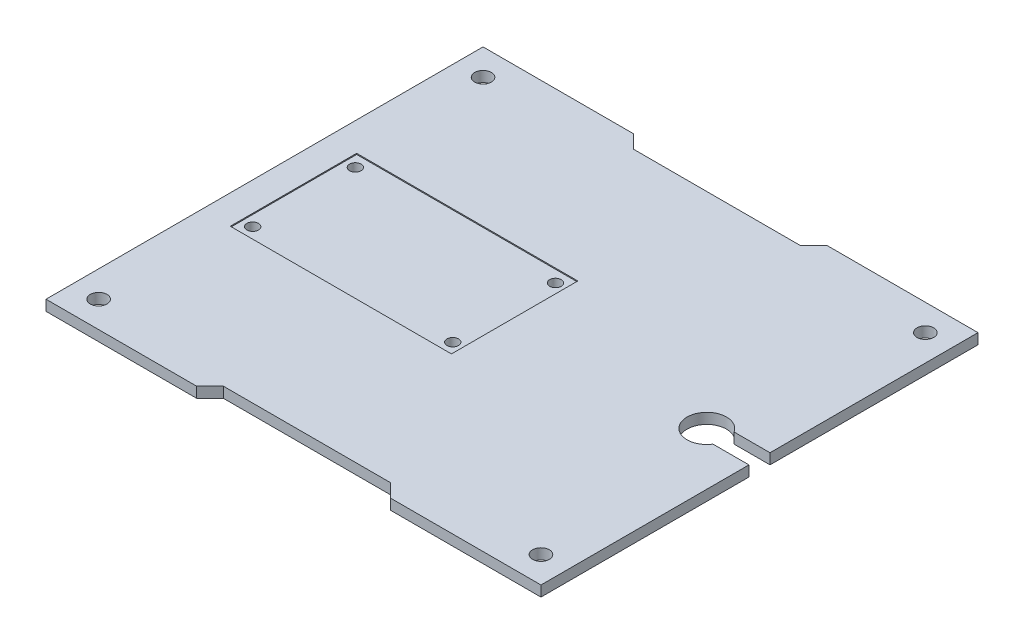
SolidWorks part; units mm, degrees
ref_plane "Front Plane" through (0, 0, 0) normal (0, 0, 1) x (1, 0, 0)
ref_plane "Top Plane" through (0, 0, 0) normal (0, 1, 0) x (1, 0, 0)
ref_plane "Right Plane" through (0, 0, 0) normal (1, 0, 0) x (0, 0, -1)
sketch "Sketch1" plane through (0, 0, 0) normal (0, 1, 0) x (1, 0, 0)
  line L1 (-47, -41.5) -> (47, -41.5)
  line L2 (-47, -41.5) -> (-47, 41.5)
  line L3 (-47, 41.5) -> (47, 41.5)
  line L4 (47, -41.5) -> (47, 41.5)
  line L5 (-47, -41.5) -> (47, 41.5) construction
  line L6 (-47, 41.5) -> (47, -41.5) construction
  line L7 (-42, -36.5) -> (42, -36.5) construction
  line L8 (-42, -36.5) -> (-42, 36.5) construction
  line L9 (-42, 36.5) -> (42, 36.5) construction
  line L10 (42, -36.5) -> (42, 36.5) construction
  line L11 (-42, -36.5) -> (42, 36.5) construction
  line L12 (-42, 36.5) -> (42, -36.5) construction
  circle A0 centre (-42, 36.5) radius 1.5875
  circle A1 centre (42, 36.5) radius 1.5875
  circle A2 centre (42, -36.5) radius 1.5875
  circle A3 centre (-42, -36.5) radius 1.5875
  point P0 (0, 0)
  point P14 (0, 0)
  dimension "D3" = 3.175
  dimension "D1" = 83
  dimension "D2" = 94
  dimension "D4" = 5
  dimension "D5" = 5
extrude "Boss-Extrude1" add sketch "Sketch1" along normal blind 2
sketch "Sketch2" plane through (0, 2, 0) normal (0, 1, 0) x (1, 0, 0)
  line L0 (0, 0) -> (-20.5, 0) construction
  line L1 (-39.5, 9.75) -> (-1.5, 9.75) construction
  line L2 (-39.5, 9.75) -> (-39.5, -9.75) construction
  line L3 (-39.5, -9.75) -> (-1.5, -9.75) construction
  line L4 (-1.5, 9.75) -> (-1.5, -9.75) construction
  line L5 (-39.5, 9.75) -> (-1.5, -9.75) construction
  line L6 (-39.5, -9.75) -> (-1.5, 9.75) construction
  line L7 (-47, 41.5) -> (-47, -41.5) construction
  line L8 (47, -41.5) -> (47, 41.5) construction
  line L9 (40.1721, 2) -> (47, 2)
  line L11 (40.1721, -2) -> (47, -2)
  line L12 (47, 2) -> (47, -2)
  line L13 (40.1721, 2) -> (47, -2) construction
  line L14 (40.1721, -2) -> (47, 2) construction
  line L15 (0, 0) -> (37, 0) construction
  line L16 (-18.415, -41.5) -> (-15.875, -38.96)
  line L17 (-47, -41.5) -> (47, -41.5) construction
  line L18 (-15.875, -38.96) -> (15.875, -38.96)
  line L19 (15.875, -38.96) -> (18.415, -41.5)
  line L20 (18.415, -41.5) -> (-18.415, -41.5)
  line L21 (-18.415, 41.5) -> (-15.875, 38.96)
  line L22 (47, 41.5) -> (-47, 41.5) construction
  line L23 (-15.875, 38.96) -> (15.875, 38.96)
  line L24 (15.875, 38.96) -> (18.415, 41.5)
  line L25 (18.415, 41.5) -> (-18.415, 41.5)
  line L26 (0, 38.96) -> (0, -38.96) construction
  circle A0 centre (-39.5, 9.75) radius 1.1
  circle A1 centre (-1.5, 9.75) radius 1.1
  circle A2 centre (-1.5, -9.75) radius 1.1
  circle A3 centre (-39.5, -9.75) radius 1.1
  arc A4 (40.1721, 2) -> (40.1721, -2) centre (37, 0) ccw
  point P4 (-20.5, 0)
  point P20 (43.5861, 0)
  point P37 (0, 0)
  point P38 (0, 0)
  dimension "D1" = 2.2
  dimension "D6" = 7.5
  dimension "D2" = 19.5
  dimension "D3" = 38
  dimension "D4" = 7.5
  dimension "D5" = 4
  dimension "D7" = 10
  dimension "D8" = 2.54
  dimension "D9" = 31.75
extrude "Cut-Extrude1" cut sketch "Sketch2" against normal blind 10
sketch "Sketch3" plane through (0, 2, 0) normal (0, 1, 0) x (1, 0, 0)
  line L0 (-39.5, 9.75) -> (-1.5, -9.75) construction
  line L1 (-41.5, 12) -> (0.5, 12)
  line L2 (-41.5, 12) -> (-41.5, -12)
  line L3 (-41.5, -12) -> (0.5, -12)
  line L4 (0.5, 12) -> (0.5, -12)
  line L5 (-41.5, 12) -> (0.5, -12) construction
  line L6 (-41.5, -12) -> (0.5, 12) construction
  line L7 (-1.5, 9.75) -> (-39.5, -9.75) construction
  point P4 (-20.5, 0)
  point P13 (0, 0)
  dimension "D1" = 24
  dimension "D2" = 42
extrude "Cut-Extrude2" cut sketch "Sketch3" against normal blind 0.2
equation "\"D5@Sketch1\"=\"D4@Sketch1\""
